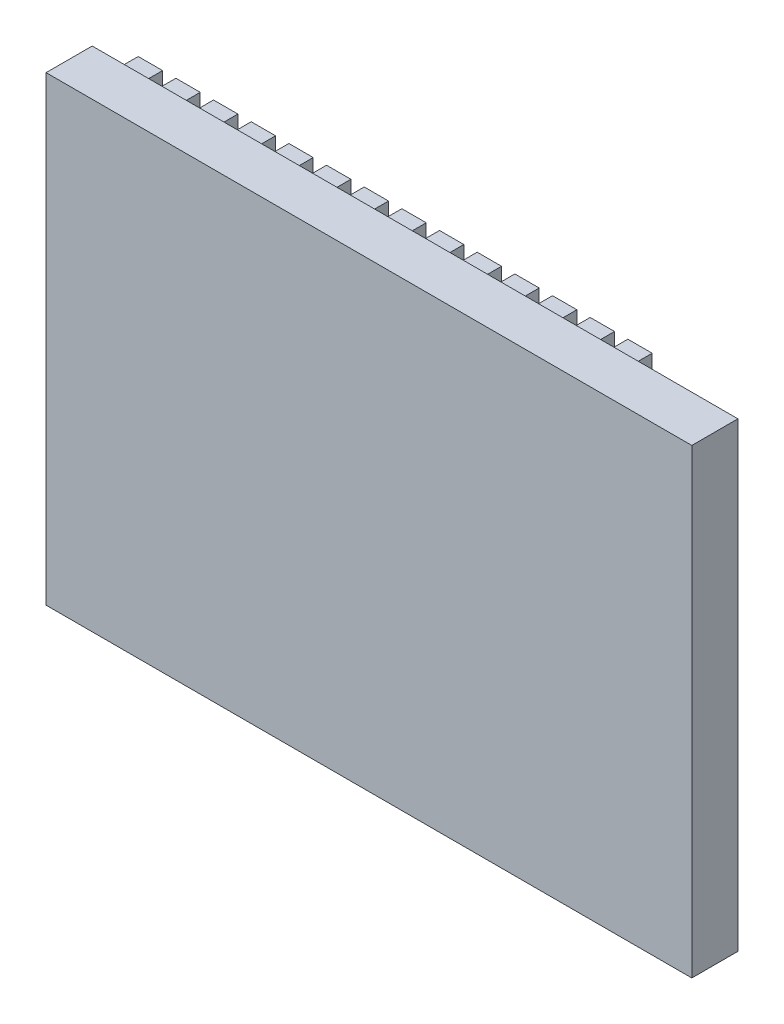
SolidWorks part; units mm, degrees
ref_plane "Front Plane" through (0, 0, 0) normal (0, 0, 1) x (1, 0, 0)
ref_plane "Top Plane" through (0, 0, 0) normal (0, 1, 0) x (1, 0, 0)
ref_plane "Right Plane" through (0, 0, 0) normal (1, 0, 0) x (0, 0, -1)
sketch "Sketch1" plane through (0, 0, 0) normal (0, 0, 1) x (1, 0, 0)
  line L1 (-30.8278, 38.8245) -> (39.1722, 38.8245)
  line L2 (-30.8278, 38.8245) -> (-30.8278, -11.1755)
  line L3 (-30.8278, -11.1755) -> (39.1722, -11.1755)
  line L4 (39.1722, 38.8245) -> (39.1722, -11.1755)
  dimension "D1" = 70
  dimension "D2" = 50
extrude "Boss-Extrude1" add sketch "Sketch1" along normal blind 5
sketch "Sketch2" plane through (0, 0, 0) normal (0, 0, -1) x (-1, 0, 0)
  line L8 (-25.8781, 36.3339) -> (-25.8781, 33.5429)
  line L9 (-25.8781, 36.3339) -> (-23.2379, 36.3339)
  line L10 (-23.2379, 36.3339) -> (-23.2379, 33.5429)
  line L11 (-25.8781, 33.5429) -> (-23.2379, 33.5429)
  line L12 (-21.7952, 36.3339) -> (-21.7952, 33.5429)
  line L13 (-21.7952, 36.3339) -> (-19.155, 36.3339)
  line L14 (-19.155, 36.3339) -> (-19.155, 33.5429)
  line L15 (-21.7952, 33.5429) -> (-19.155, 33.5429)
  line L16 (-17.7123, 36.3339) -> (-17.7123, 33.5429)
  line L17 (-17.7123, 36.3339) -> (-15.0722, 36.3339)
  line L18 (-15.0722, 36.3339) -> (-15.0722, 33.5429)
  line L19 (-17.7123, 33.5429) -> (-15.0722, 33.5429)
  line L20 (-13.6295, 36.3339) -> (-13.6295, 33.5429)
  line L21 (-13.6295, 36.3339) -> (-10.9893, 36.3339)
  line L22 (-10.9893, 36.3339) -> (-10.9893, 33.5429)
  line L23 (-13.6295, 33.5429) -> (-10.9893, 33.5429)
  line L24 (-9.5466, 36.3339) -> (-9.5466, 33.5429)
  line L25 (-9.5466, 36.3339) -> (-6.9064, 36.3339)
  line L26 (-6.9064, 36.3339) -> (-6.9064, 33.5429)
  line L27 (-9.5466, 33.5429) -> (-6.9064, 33.5429)
  line L28 (-5.4637, 36.3339) -> (-5.4637, 33.5429)
  line L29 (-5.4637, 36.3339) -> (-2.8235, 36.3339)
  line L30 (-2.8235, 36.3339) -> (-2.8235, 33.5429)
  line L31 (-5.4637, 33.5429) -> (-2.8235, 33.5429)
  line L32 (-1.3808, 36.3339) -> (-1.3808, 33.5429)
  line L33 (-1.3808, 36.3339) -> (1.2593, 36.3339)
  line L34 (1.2593, 36.3339) -> (1.2593, 33.5429)
  line L35 (-1.3808, 33.5429) -> (1.2593, 33.5429)
  line L36 (2.702, 36.3339) -> (2.702, 33.5429)
  line L37 (2.702, 36.3339) -> (5.3422, 36.3339)
  line L38 (5.3422, 36.3339) -> (5.3422, 33.5429)
  line L39 (2.702, 33.5429) -> (5.3422, 33.5429)
  line L40 (6.7849, 36.3339) -> (6.7849, 33.5429)
  line L41 (6.7849, 36.3339) -> (9.4251, 36.3339)
  line L42 (9.4251, 36.3339) -> (9.4251, 33.5429)
  line L43 (6.7849, 33.5429) -> (9.4251, 33.5429)
  line L44 (10.8678, 36.3339) -> (10.8678, 33.5429)
  line L45 (10.8678, 36.3339) -> (13.508, 36.3339)
  line L46 (13.508, 36.3339) -> (13.508, 33.5429)
  line L47 (10.8678, 33.5429) -> (13.508, 33.5429)
  line L48 (14.9507, 36.3339) -> (14.9507, 33.5429)
  line L49 (14.9507, 36.3339) -> (17.5908, 36.3339)
  line L50 (17.5908, 36.3339) -> (17.5908, 33.5429)
  line L51 (14.9507, 33.5429) -> (17.5908, 33.5429)
  line L52 (19.0335, 36.3339) -> (19.0335, 33.5429)
  line L53 (19.0335, 36.3339) -> (21.6737, 36.3339)
  line L54 (21.6737, 36.3339) -> (21.6737, 33.5429)
  line L55 (19.0335, 33.5429) -> (21.6737, 33.5429)
  line L56 (23.1164, 36.3339) -> (23.1164, 33.5429)
  line L57 (23.1164, 36.3339) -> (25.7566, 36.3339)
  line L58 (25.7566, 36.3339) -> (25.7566, 33.5429)
  line L59 (23.1164, 33.5429) -> (25.7566, 33.5429)
  line L60 (27.1993, 36.3339) -> (27.1993, 33.5429)
  line L61 (27.1993, 36.3339) -> (29.8395, 36.3339)
  line L62 (29.8395, 36.3339) -> (29.8395, 33.5429)
  line L63 (27.1993, 33.5429) -> (29.8395, 33.5429)
  line L68 (-26.4065, -6.6628) -> (-26.4065, -9.4538)
  line L69 (-26.4065, -6.6628) -> (-23.7664, -6.6628)
  line L70 (-23.7664, -6.6628) -> (-23.7664, -9.4538)
  line L71 (-26.4065, -9.4538) -> (-23.7664, -9.4538)
  line L72 (-22.3237, -6.6628) -> (-22.3237, -9.4538)
  line L73 (-22.3237, -6.6628) -> (-19.6835, -6.6628)
  line L74 (-19.6835, -6.6628) -> (-19.6835, -9.4538)
  line L75 (-22.3237, -9.4538) -> (-19.6835, -9.4538)
  line L76 (-18.2408, -6.6628) -> (-18.2408, -9.4538)
  line L77 (-18.2408, -6.6628) -> (-15.6006, -6.6628)
  line L78 (-15.6006, -6.6628) -> (-15.6006, -9.4538)
  line L79 (-18.2408, -9.4538) -> (-15.6006, -9.4538)
  line L80 (-14.1579, -6.6628) -> (-14.1579, -9.4538)
  line L81 (-14.1579, -6.6628) -> (-11.5177, -6.6628)
  line L82 (-11.5177, -6.6628) -> (-11.5177, -9.4538)
  line L83 (-14.1579, -9.4538) -> (-11.5177, -9.4538)
  line L84 (-10.075, -6.6628) -> (-10.075, -9.4538)
  line L85 (-10.075, -6.6628) -> (-7.4349, -6.6628)
  line L86 (-7.4349, -6.6628) -> (-7.4349, -9.4538)
  line L87 (-10.075, -9.4538) -> (-7.4349, -9.4538)
  line L96 (2.1736, -6.6628) -> (2.1736, -9.4538)
  line L97 (2.1736, -6.6628) -> (4.8138, -6.6628)
  line L98 (4.8138, -6.6628) -> (4.8138, -9.4538)
  line L99 (2.1736, -9.4538) -> (4.8138, -9.4538)
  line L100 (6.2565, -6.6628) -> (6.2565, -9.4538)
  line L101 (6.2565, -6.6628) -> (8.8966, -6.6628)
  line L102 (8.8966, -6.6628) -> (8.8966, -9.4538)
  line L103 (6.2565, -9.4538) -> (8.8966, -9.4538)
  line L104 (10.3393, -6.6628) -> (10.3393, -9.4538)
  line L105 (10.3393, -6.6628) -> (12.9795, -6.6628)
  line L106 (12.9795, -6.6628) -> (12.9795, -9.4538)
  line L107 (10.3393, -9.4538) -> (12.9795, -9.4538)
  line L108 (14.4222, -6.6628) -> (14.4222, -9.4538)
  line L109 (14.4222, -6.6628) -> (17.0624, -6.6628)
  line L110 (17.0624, -6.6628) -> (17.0624, -9.4538)
  line L111 (14.4222, -9.4538) -> (17.0624, -9.4538)
  line L112 (18.5051, -6.6628) -> (18.5051, -9.4538)
  line L113 (18.5051, -6.6628) -> (21.1453, -6.6628)
  line L114 (21.1453, -6.6628) -> (21.1453, -9.4538)
  line L115 (18.5051, -9.4538) -> (21.1453, -9.4538)
  line L116 (22.588, -6.6628) -> (22.588, -9.4538)
  line L117 (22.588, -6.6628) -> (25.2281, -6.6628)
  line L118 (25.2281, -6.6628) -> (25.2281, -9.4538)
  line L119 (22.588, -9.4538) -> (25.2281, -9.4538)
  line L120 (26.6708, -6.6628) -> (26.6708, -9.4538)
  line L121 (26.6708, -6.6628) -> (29.311, -6.6628)
  line L122 (29.311, -6.6628) -> (29.311, -9.4538)
  line L123 (26.6708, -9.4538) -> (29.311, -9.4538)
  point P4 (0, 0)
extrude "Boss-Extrude2" add sketch "Sketch2" along normal blind 4
sketch "Sketch3" plane through (0, 0, 0) normal (0, 0, -1) x (-1, 0, 0)
  line L1 (15.4405, 23.5302) -> (26.9064, 23.5302)
  line L2 (15.4405, 23.5302) -> (15.4405, 1.73)
  line L3 (15.4405, 1.73) -> (26.9064, 1.73)
  line L4 (26.9064, 23.5302) -> (26.9064, 1.73)
  line L5 (-37.1366, 36.1276) -> (-29.367, 36.1276)
  line L6 (-37.1366, 36.1276) -> (-37.1366, -8.9816)
  line L7 (-37.1366, -8.9816) -> (-29.367, -8.9816)
  line L8 (-29.367, 36.1276) -> (-29.367, -8.9816)
extrude "Cut-Extrude2" cut sketch "Sketch3" against normal blind 2 contours L6 L5 L8 L7
sketch "Sketch4" plane through (0, 0, 0) normal (0, 0, -1) x (-1, 0, 0)
  line L1 (9.8584, 25.4035) -> (22.833, 25.4035)
  line L2 (9.8584, 25.4035) -> (9.8584, 2.3963)
  line L3 (9.8584, 2.3963) -> (22.833, 2.3963)
  line L4 (22.833, 25.4035) -> (22.833, 2.3963)
extrude "Boss-Extrude3" add sketch "Sketch4" along normal blind 4
